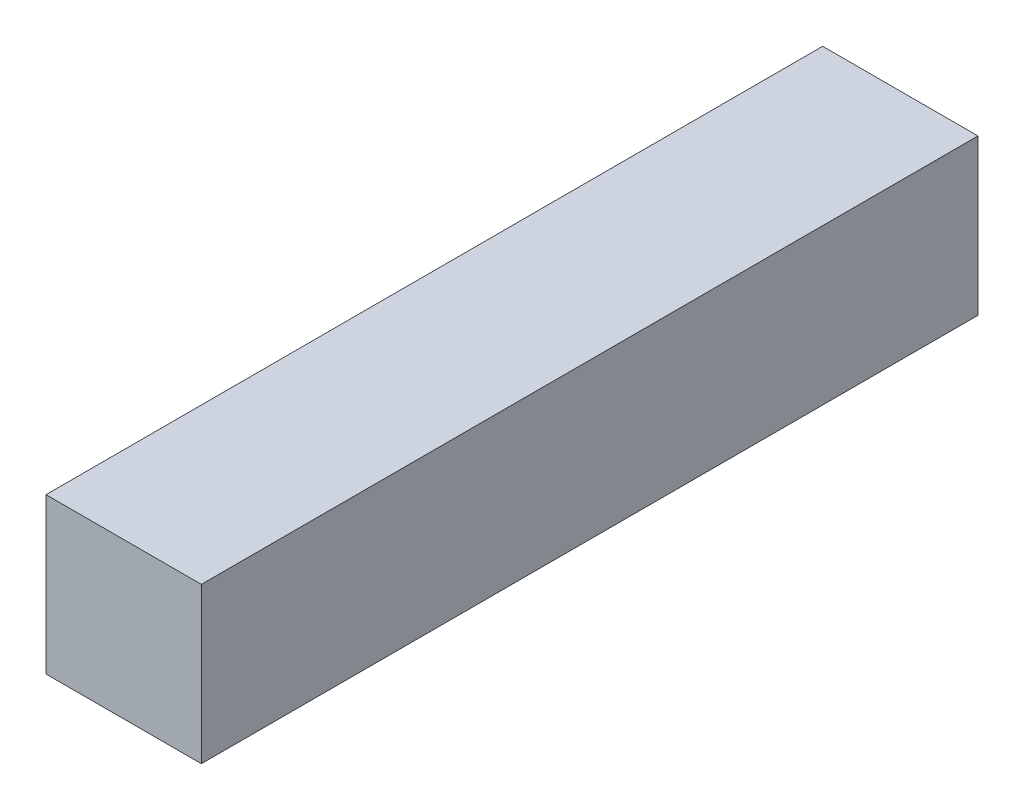
SolidWorks part; units mm, degrees
ref_plane "Front Plane" through (0, 0, 0) normal (0, 0, 1) x (1, 0, 0)
ref_plane "Top Plane" through (0, 0, 0) normal (0, 1, 0) x (1, 0, 0)
ref_plane "Right Plane" through (0, 0, 0) normal (1, 0, 0) x (0, 0, -1)
sketch "Sketch1" plane through (0, 0, 0) normal (0, 1, 0) x (1, 0, 0)
  line L1 (-2.54, 12.7) -> (2.54, 12.7)
  line L2 (-2.54, 12.7) -> (-2.54, -12.7)
  line L3 (-2.54, -12.7) -> (2.54, -12.7)
  line L4 (2.54, 12.7) -> (2.54, -12.7)
  line L5 (-2.54, 12.7) -> (2.54, -12.7) construction
  line L6 (-2.54, -12.7) -> (2.54, 12.7) construction
  point P0 (0, 0)
  dimension "D1" = 25.4
  dimension "D2" = 5.08
extrude "Boss-Extrude1" add sketch "Sketch1" along normal blind 5.08
